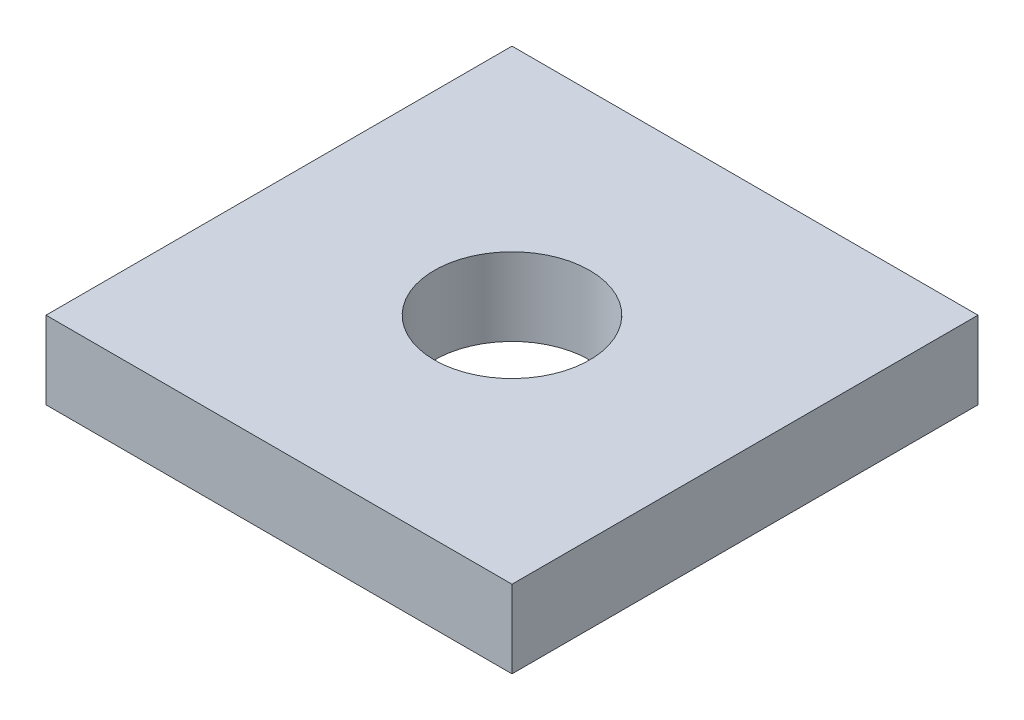
SolidWorks part; units mm, degrees
ref_plane "Front Plane" through (0, 0, 0) normal (0, 0, 1) x (1, 0, 0)
ref_plane "Top Plane" through (0, 0, 0) normal (0, 1, 0) x (1, 0, 0)
ref_plane "Right Plane" through (0, 0, 0) normal (1, 0, 0) x (0, 0, -1)
sketch "Sketch1" plane through (0, 0, 0) normal (0, 1, 0) x (1, 0, 0)
  line L1 (0, 0) -> (76.2, 0)
  line L2 (0, 0) -> (0, 76.2)
  line L3 (0, 76.2) -> (76.2, 76.2)
  line L4 (76.2, 0) -> (76.2, 76.2)
  dimension "D1" = 76.2
  dimension "D2" = 76.2
extrude "Boss-Extrude1" add sketch "Sketch1" along normal blind 12.7
sketch "Sketch2" plane through (0, 12.7, 0) normal (0, 1, 0) x (-1, 0, 0)
  line L1 (0, -38.1) -> (-76.2, -38.1) construction
  line L2 (0, -76.2) -> (0, 0) construction
  line L3 (-76.2, 0) -> (-76.2, -76.2) construction
  line L5 (0, 0) -> (-76.2, 0) construction
  line L6 (-38.1, 0) -> (-38.1, -76.2) construction
  line L7 (-76.2, -76.2) -> (0, -76.2) construction
  circle A0 centre (-38.1, -38.1) radius 12.7
  dimension "D1" = 25.4
extrude "Cut-Extrude1" cut sketch "Sketch2" against normal up to next
